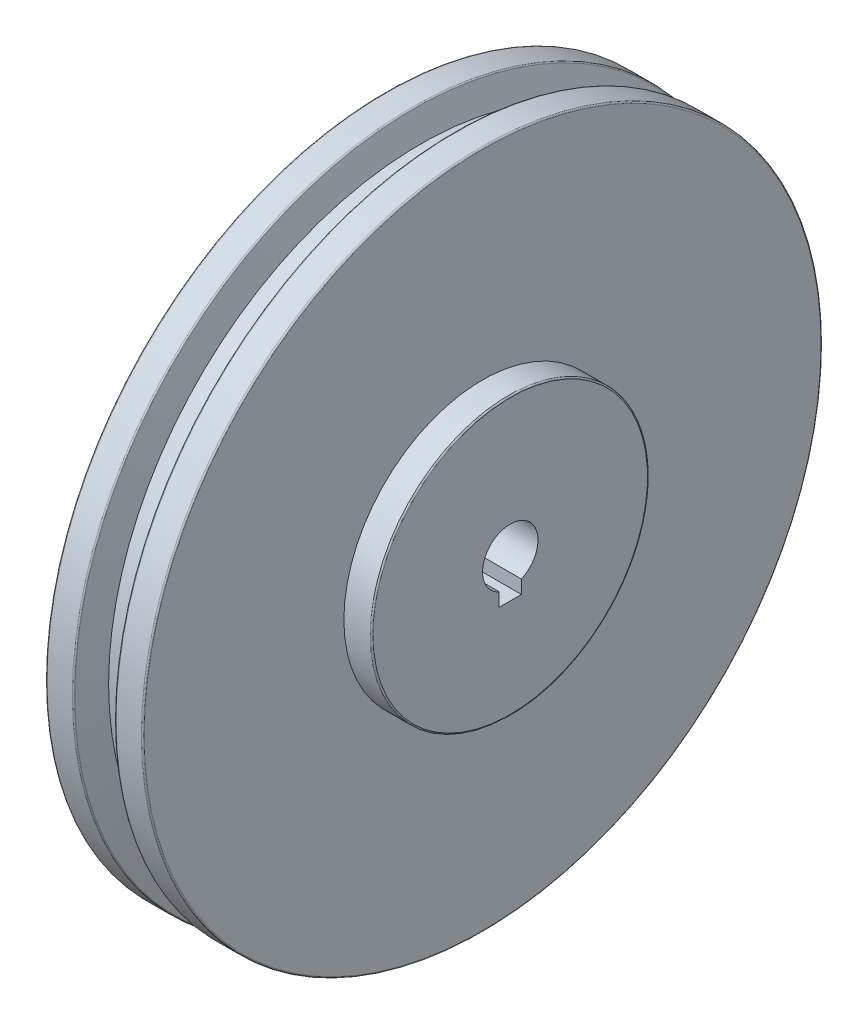
SolidWorks part; units mm, degrees
ref_plane "Front Plane" through (0, 0, 0) normal (0, 0, 1) x (1, 0, 0)
ref_plane "Top Plane" through (0, 0, 0) normal (0, 1, 0) x (1, 0, 0)
ref_plane "Right Plane" through (0, 0, 0) normal (1, 0, 0) x (0, 0, -1)
sketch "Sketch1" plane through (0, 0, 0) normal (0, 0, 1) x (1, 0, 0)
  line L0 (0, 0) -> (43.9763, 0) construction
  line L1 (0, -20) -> (0, -122)
  line L2 (0.5, -122.5) -> (9.6163, -122.5)
  line L3 (10.0993, -122.1294) -> (12.6795, -112.5)
  line L4 (12.6795, -112.5) -> (22.3205, -112.5)
  line L5 (22.3205, -112.5) -> (24.9007, -122.1294)
  line L6 (25.3837, -122.5) -> (34.5, -122.5)
  line L7 (35, -122) -> (35, -50)
  line L8 (35, -50) -> (44.5, -50)
  line L9 (45, -49.5) -> (45, -10)
  line L10 (45, -10) -> (2.5, -10)
  line L11 (0, -20) -> (2.5, -10)
  arc A0 (44.5, -50) -> (45, -49.5) centre (44.5, -49.5) ccw
  arc A1 (34.5, -122.5) -> (35, -122) centre (34.5, -122) ccw
  arc A2 (24.9007, -122.1294) -> (25.3837, -122.5) centre (25.3837, -122) ccw
  arc A3 (9.6163, -122.5) -> (10.0993, -122.1294) centre (9.6163, -122) ccw
  arc A4 (0, -122) -> (0.5, -122.5) centre (0.5, -122) ccw
  point P18 (35, -122.5)
  point P21 (25, -122.5)
  point P24 (10, -122.5)
  point P27 (0, -122.5)
  dimension "D14" = 100
  dimension "D15" = 0.5
  dimension "D10" = 0.5
  dimension "D1" = 20
  dimension "D2" = 245
  dimension "D3" = 225
  dimension "D4" = 245
  dimension "D5" = 105
  dimension "D6" = 10
  dimension "D7" = 10
  dimension "D8" = 15
  dimension "D9" = 105
  dimension "D11" = 45
  dimension "D12" = 2.5
  dimension "D13" = 10
revolve "Revolve1" add sketch "Sketch1" angle 360 about L0
sketch "Esboço1" plane through (0, 0, 0) normal (-1, 0, 0) x (0, 0, 1)
  line L0 (0, 0) -> (0, -10) construction
  line L1 (4, -14) -> (-4, -14)
  line L2 (4, -14) -> (4, -6)
  line L3 (4, -6) -> (-4, -6)
  line L4 (-4, -14) -> (-4, -6)
  line L5 (4, -14) -> (-4, -6) construction
  line L6 (4, -6) -> (-4, -14) construction
  circle A0 centre (0, 0) radius 10 construction
  point P0 (0, -10)
  dimension "D1" = 8
  dimension "D2" = 8
extrude "Corte-extrusão1" cut sketch "Esboço1" against normal through all
